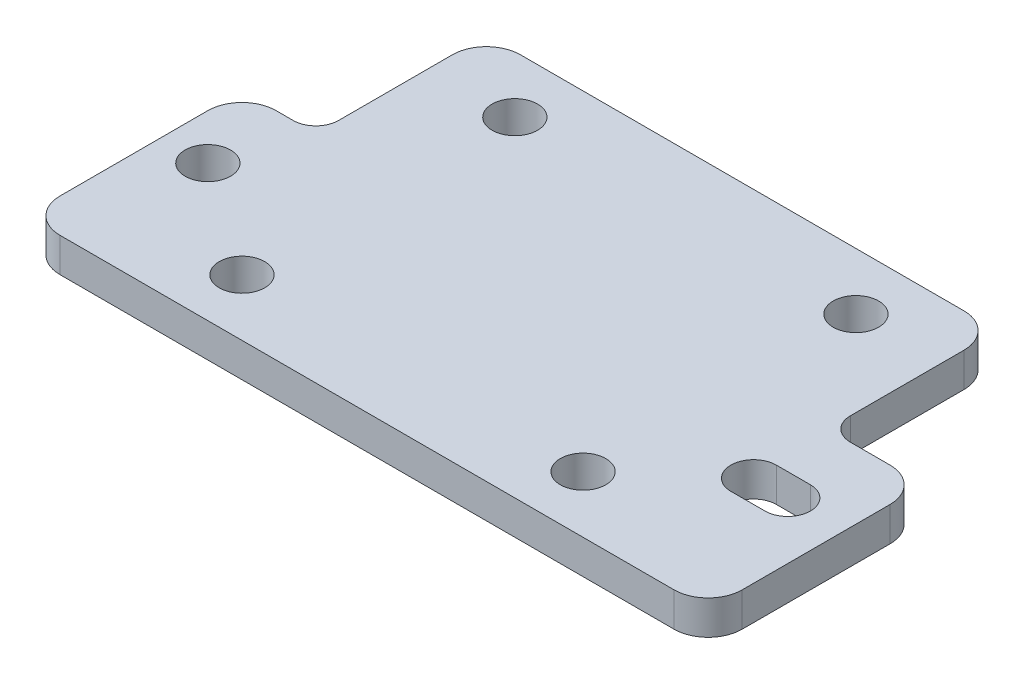
SolidWorks part; units mm, degrees
material "1060 Alloy"
ref_plane "Front Plane" through (0, 0, 0) normal (0, 0, 1) x (1, 0, 0)
ref_plane "Top Plane" through (0, 0, 0) normal (0, 1, 0) x (1, 0, 0)
ref_plane "Right Plane" through (0, 0, 0) normal (1, 0, 0) x (0, 0, -1)
sketch "Sketch1" plane through (0, 0, 0) normal (0, 1, 0) x (1, 0, 0)
  line L0 (0, 17) -> (0, -17) construction
  line L1 (-22.5, -17) -> (22.5, -17)
  line L2 (-22.5, -17) -> (-22.5, 17)
  line L3 (-22.5, 17) -> (22.5, 17)
  line L4 (22.5, -17) -> (22.5, 17)
  line L5 (-22.5, -17) -> (22.5, 17) construction
  line L6 (-22.5, 17) -> (22.5, -17) construction
  line L7 (-29, -17) -> (31, -17)
  line L8 (-29, -17) -> (-29, 2)
  line L9 (-29, 2) -> (31, 2)
  line L10 (31, -17) -> (31, 2)
  line L11 (-22.5, 0) -> (22.5, 0) construction
  line L12 (23, -5) -> (26, -5) construction
  line L13 (23, -3) -> (26, -3)
  line L14 (23, -7) -> (26, -7)
  circle A0 centre (-15, 12) radius 2
  circle A1 centre (15, 12) radius 2
  circle A2 centre (15, -12) radius 2
  circle A3 centre (-15, -12) radius 2
  circle A4 centre (-25, -5) radius 2
  arc A5 (23, -3) -> (23, -7) centre (23, -5) ccw
  arc A6 (26, -7) -> (26, -3) centre (26, -5) ccw
  point P0 (0, 0)
  point P26 (24.5, -5)
  dimension "D6" = 12
  dimension "D7" = 4
  dimension "D8" = 14
  dimension "D9" = 4
  dimension "D10" = 2
  dimension "D12" = 4
  dimension "D1" = 34
  dimension "D2" = 45
  dimension "D3" = 19
  dimension "D4" = 60
  dimension "D5" = 15
  dimension "D11" = 7
  dimension "D13" = 5
  dimension "D14" = 3
extrude "Boss-Extrude1" add sketch "Sketch1" along normal blind 3 contours A5 L4 L9 L2 L1 A2 A3 | L9 L8 L7 L2 A4 | L2 L9 L4 L3 A0 A1 | A6 L14 A5 L4 L7 L10 L9 L13
fillet "Fillet1" radius 3 6 edges at (-29, 1.5, 17) (-29, 1.5, -2) (-22.5, 1.5, -17) (31, 1.5, -2) (22.5, 1.5, -17) (31, 1.5, 17)
fillet "Fillet2" radius 2 2 edges at (-22.5, 1.5, -2) (22.5, 1.5, -2)
